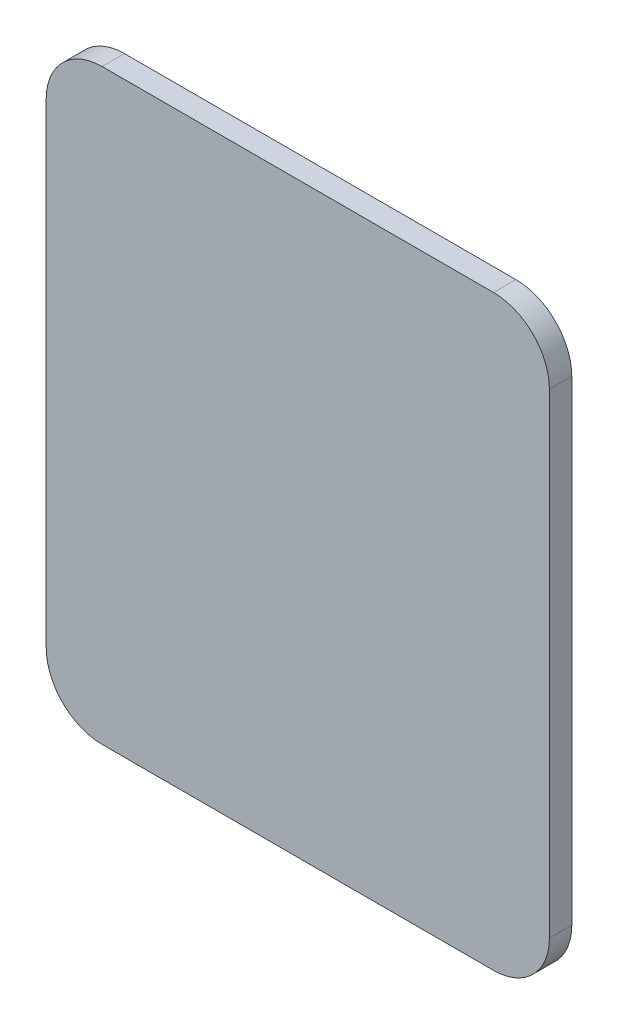
SolidWorks part; units mm, degrees
ref_plane "Front Plane" through (0, 0, 0) normal (0, 0, 1) x (1, 0, 0)
ref_plane "Top Plane" through (0, 0, 0) normal (0, 1, 0) x (1, 0, 0)
ref_plane "Right Plane" through (0, 0, 0) normal (1, 0, 0) x (0, 0, -1)
sketch "Эскиз1" plane through (0, 0, 0) normal (0, 0, 1) x (1, 0, 0)
  line L1 (-9, -10.5) -> (9, -10.5)
  line L2 (-9, -10.5) -> (-9, 10.5)
  line L3 (-9, 10.5) -> (9, 10.5)
  line L4 (9, -10.5) -> (9, 10.5)
  line L5 (-9, -10.5) -> (9, 10.5) construction
  line L6 (-9, 10.5) -> (9, -10.5) construction
  point P0 (0, 0)
  dimension "D1" = 18
  dimension "D2" = 21
extrude "Бобышка-Вытянуть1" add sketch "Эскиз1" along normal mid plane 0.8
fillet "Скругление1" radius 2 4 edges at (-9, -10.5, 0) (9, -10.5, 0) (-9, 10.5, 0) (9, 10.5, 0)
